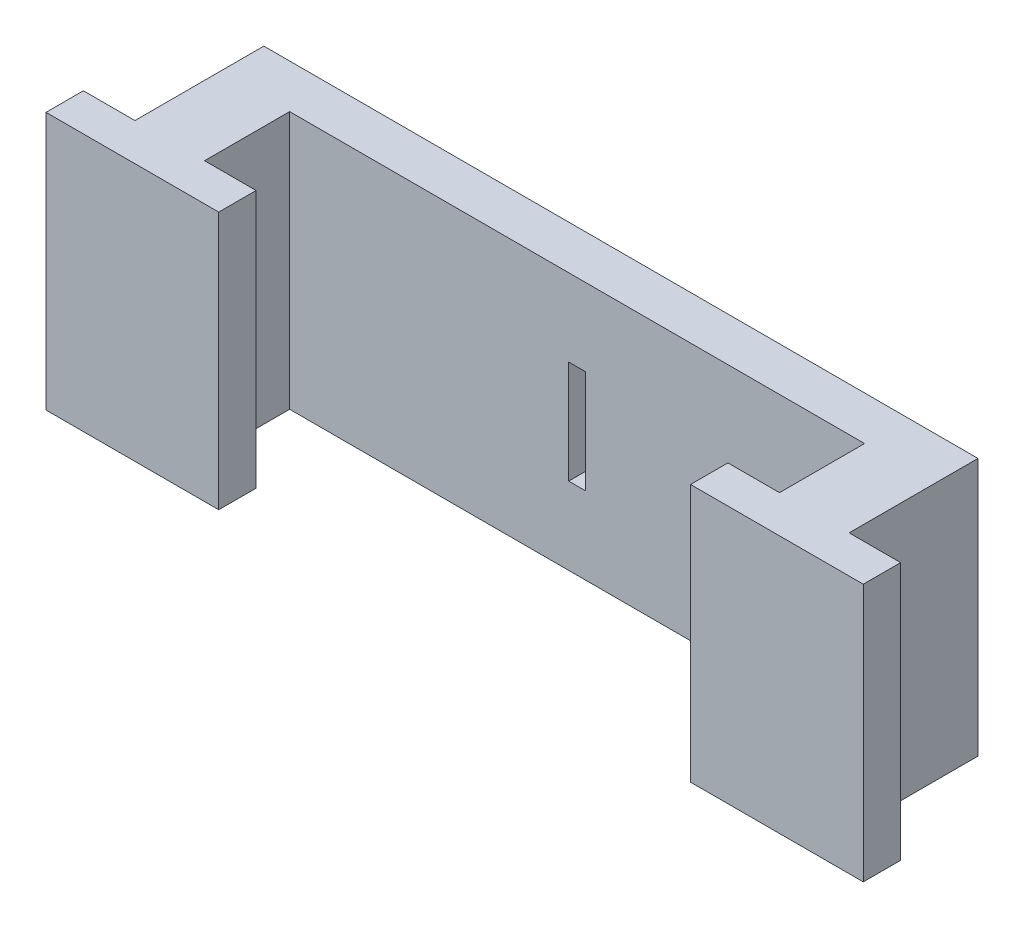
SolidWorks part; units mm, degrees
ref_plane "Front Plane" through (0, 0, 0) normal (0, 0, 1) x (1, 0, 0)
ref_plane "Top Plane" through (0, 0, 0) normal (0, 1, 0) x (1, 0, 0)
ref_plane "Right Plane" through (0, 0, 0) normal (1, 0, 0) x (0, 0, -1)
sketch "Sketch1" plane through (0, 0, 0) normal (0, 1, 0) x (1, 0, 0)
  line L0 (1.5, 1.75) -> (3.5, 1.75)
  line L1 (-3.5, 1.75) -> (-1.5, 1.75)
  line L2 (-3.5, 1.75) -> (-3.5, 0)
  line L3 (-3.5, 0) -> (3.5, 0)
  line L4 (3.5, 1.75) -> (3.5, 0)
  line L5 (-1.5, 6.75) -> (1.5, 6.75)
  line L6 (-1.5, 6.75) -> (-1.5, 1.75)
  line L8 (1.5, 4.75) -> (1.5, 1.75)
  line L9 (0, 0) -> (0, 6.75) construction
  line L10 (0, 0) -> (25, 0) construction
  line L11 (12.5, 0) -> (12.5, 6.15) construction
  line L12 (25, 0) -> (25, 6.75) construction
  line L13 (23.5, 4.75) -> (23.5, 1.75)
  line L14 (26.5, 6.75) -> (26.5, 1.75)
  line L15 (26.5, 6.75) -> (23.5, 6.75)
  line L16 (21.5, 1.75) -> (21.5, 0)
  line L17 (28.5, 0) -> (21.5, 0)
  line L18 (28.5, 1.75) -> (28.5, 0)
  line L19 (28.5, 1.75) -> (26.5, 1.75)
  line L20 (23.5, 1.75) -> (21.5, 1.75)
  line L21 (1.5, 6.75) -> (23.5, 6.75)
  line L22 (1.5, 4.75) -> (23.5, 4.75)
  point P5 (0, 0)
  dimension "D1" = 2
  dimension "D2" = 3
  dimension "D3" = 1.75
  dimension "D4" = 5
  dimension "D5" = 25
  dimension "D6" = 2
extrude "Boss-Extrude1" add sketch "Sketch1" along normal blind 10
sketch "Sketch2" plane through (0, 10, 0) normal (0, 1, 0) x (1, 0, 0)
  line L48 (-3.35, 1.6) -> (-3.35, 0.15)
  line L49 (-3.35, 0.15) -> (3.35, 0.15)
  line L50 (3.35, 0.15) -> (3.35, 1.6)
  line L51 (3.35, 1.6) -> (1.35, 1.6)
  line L52 (1.35, 1.6) -> (1.35, 4.9)
  line L53 (1.35, 4.9) -> (23.65, 4.9)
  line L54 (23.65, 4.9) -> (23.65, 1.6)
  line L55 (23.65, 1.6) -> (21.65, 1.6)
  line L56 (21.65, 1.6) -> (21.65, 0.15)
  line L57 (21.65, 0.15) -> (28.35, 0.15)
  line L58 (28.35, 0.15) -> (28.35, 1.6)
  line L59 (28.35, 1.6) -> (26.35, 1.6)
  line L60 (26.35, 1.6) -> (26.35, 6.6)
  line L61 (26.35, 6.6) -> (-1.35, 6.6)
  line L62 (-1.35, 6.6) -> (-1.35, 1.6)
  line L63 (-1.35, 1.6) -> (-3.35, 1.6)
  line L64 (-3.35, 1.6) -> (-3.35, 0.15)
  line L65 (-3.35, 0.15) -> (3.35, 0.15)
  line L66 (3.35, 0.15) -> (3.35, 1.6)
  line L67 (3.35, 1.6) -> (1.35, 1.6)
  line L68 (1.35, 1.6) -> (1.35, 4.9)
  line L69 (1.35, 4.9) -> (23.65, 4.9)
  line L70 (23.65, 4.9) -> (23.65, 1.6)
  line L71 (23.65, 1.6) -> (21.65, 1.6)
  line L72 (21.65, 1.6) -> (21.65, 0.15)
  line L73 (21.65, 0.15) -> (28.35, 0.15)
  line L74 (28.35, 0.15) -> (28.35, 1.6)
  line L75 (28.35, 1.6) -> (26.35, 1.6)
  line L76 (26.35, 1.6) -> (26.35, 6.6)
  line L77 (26.35, 6.6) -> (-1.35, 6.6)
  line L78 (-1.35, 6.6) -> (-1.35, 1.6)
  line L79 (-1.35, 1.6) -> (-3.35, 1.6)
  line L96 (-3.65, 1.9) -> (-3.65, -0.15)
  line L97 (-3.65, -0.15) -> (3.65, -0.15)
  line L98 (3.65, -0.15) -> (3.65, 1.9)
  line L99 (3.65, 1.9) -> (1.65, 1.9)
  line L100 (1.65, 1.9) -> (1.65, 4.6)
  line L101 (1.65, 4.6) -> (23.35, 4.6)
  line L102 (23.35, 4.6) -> (23.35, 1.9)
  line L103 (23.35, 1.9) -> (21.35, 1.9)
  line L104 (21.35, 1.9) -> (21.35, -0.15)
  line L105 (21.35, -0.15) -> (28.65, -0.15)
  line L106 (28.65, -0.15) -> (28.65, 1.9)
  line L107 (28.65, 1.9) -> (26.65, 1.9)
  line L108 (26.65, 1.9) -> (26.65, 6.9)
  line L109 (26.65, 6.9) -> (-1.65, 6.9)
  line L110 (-1.65, 6.9) -> (-1.65, 1.9)
  line L111 (-1.65, 1.9) -> (-3.65, 1.9)
  line L112 (-3.65, 1.9) -> (-3.65, -0.15)
  line L113 (-3.65, -0.15) -> (3.65, -0.15)
  line L114 (3.65, -0.15) -> (3.65, 1.9)
  line L115 (3.65, 1.9) -> (1.65, 1.9)
  line L116 (1.65, 1.9) -> (1.65, 4.6)
  line L117 (1.65, 4.6) -> (23.35, 4.6)
  line L118 (23.35, 4.6) -> (23.35, 1.9)
  line L119 (23.35, 1.9) -> (21.35, 1.9)
  line L120 (21.35, 1.9) -> (21.35, -0.15)
  line L121 (21.35, -0.15) -> (28.65, -0.15)
  line L122 (28.65, -0.15) -> (28.65, 1.9)
  line L123 (28.65, 1.9) -> (26.65, 1.9)
  line L124 (26.65, 1.9) -> (26.65, 6.9)
  line L125 (26.65, 6.9) -> (-1.65, 6.9)
  line L126 (-1.65, 6.9) -> (-1.65, 1.9)
  line L127 (-1.65, 1.9) -> (-3.65, 1.9)
  dimension "D1" = 0.15
  dimension "D2" = 0.15
extrude "Cut-Extrude2" cut sketch "Sketch2" against normal through all
sketch "Sketch3" plane through (0, 0, -6.6) normal (0, 0, -1) x (-1, 0, 0)
  line L0 (-12.5, 0) -> (-12.5, 10) construction
  line L1 (-26.35, 0) -> (1.35, 0) construction
  line L2 (-26.35, 10) -> (1.35, 10) construction
  line L3 (1.35, 5) -> (-26.35, 5) construction
  line L4 (-12.175, 3) -> (-12.825, 3)
  line L5 (-12.175, 3) -> (-12.175, 7)
  line L6 (-12.175, 7) -> (-12.825, 7)
  line L7 (-12.825, 3) -> (-12.825, 7)
  line L8 (1.35, 0) -> (1.35, 10) construction
  line L9 (-26.35, 0) -> (-26.35, 10) construction
  point P10 (-12.5, 3)
  point P17 (-12.825, 5)
  dimension "D1" = 4
  dimension "D2" = 0.65
extrude "Cut-Extrude3" cut sketch "Sketch3" against normal through all
